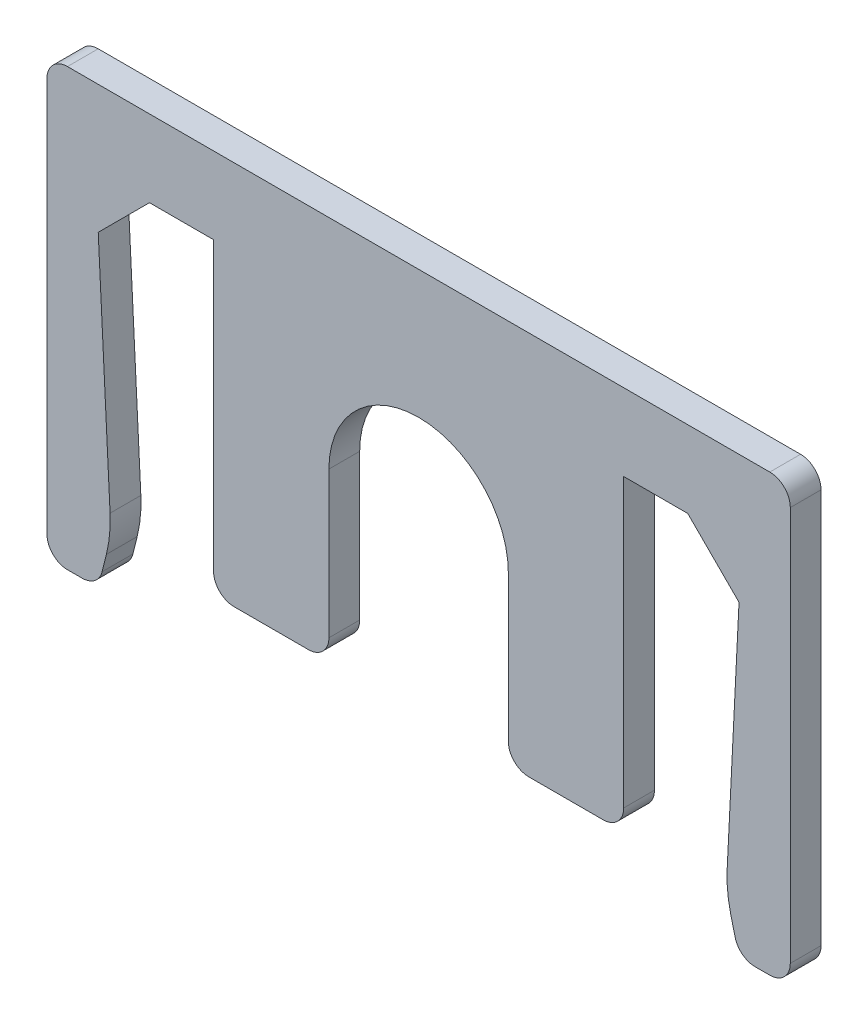
SolidWorks part; units mm, degrees
ref_plane "Front Plane" through (0, 0, 0) normal (0, 0, 1) x (1, 0, 0)
ref_plane "Top Plane" through (0, 0, 0) normal (0, 1, 0) x (1, 0, 0)
ref_plane "Right Plane" through (0, 0, 0) normal (1, 0, 0) x (0, 0, -1)
sketch "Sketch1" plane through (0, 0, 0) normal (0, 0, 1) x (1, 0, 0)
  line L0 (-12.5, 0) -> (-10.5, 0) construction
  line L1 (-10.5, 0) -> (-12.5, -2)
  line L2 (-12.5, -2) -> (-12.5, 0) construction
  line L3 (12.5, 0) -> (12.5, -2) construction
  line L4 (12.5, -2) -> (10.5, 0)
  line L5 (10.5, 0) -> (12.5, 0) construction
  line L6 (-12.5, -2) -> (-12, -12)
  line L7 (-12, -12) -> (-12.5, -14)
  line L8 (-12.5, -14) -> (-12.5, -2) construction
  line L9 (12.5, -2) -> (12.5, -14) construction
  line L10 (12.5, -14) -> (12, -12)
  line L11 (12, -12) -> (12.5, -2)
  line L12 (-10.5, 0) -> (-8, 0) construction
  line L13 (-3.5, -12) -> (3.5, -12) construction
  line L14 (-12.5, -14) -> (-14.5, -14)
  line L15 (-12.5, -14) -> (-12.5, -2) construction
  line L16 (-12.5, 3) -> (-14.5, 3)
  line L17 (-14.5, -14) -> (-14.5, 3)
  line L18 (12.5, -14) -> (14.5, -14)
  line L19 (12.5, -14) -> (12.5, -2) construction
  line L20 (12.5, 3) -> (14.5, 3)
  line L21 (14.5, -14) -> (14.5, 3)
  line L22 (-12.5, 3) -> (12.5, 3)
  line L23 (-12.5, 3) -> (-12.5, 0) construction
  line L24 (-10.5, 0) -> (-8, 0)
  line L25 (12.5, 3) -> (12.5, 0) construction
  line L26 (-3.5, -5.5) -> (3.5, -5.5) construction
  line L27 (-3.5, -5.5) -> (-3.5, -12)
  line L28 (-3.5, -12) -> (3.5, -12) construction
  line L29 (3.5, -5.5) -> (3.5, -12)
  line L30 (-8, -12) -> (-3.5, -12)
  line L31 (-8, -12) -> (-8, 0)
  line L32 (-8, 0) -> (8, 0) construction
  line L33 (8, -12) -> (8, 0)
  line L34 (-4.5, -3) -> (4.5, -3) construction
  line L35 (-4.5, -3) -> (-4.5, -12) construction
  line L36 (-4.5, -12) -> (-3.5, -12) construction
  line L37 (4.5, -3) -> (4.5, -12) construction
  line L38 (-4.5, -3) -> (4.5, -12) construction
  line L39 (-4.5, -12) -> (4.5, -3) construction
  line L40 (3.5, -12) -> (8, -12)
  line L41 (-3.5, -12) -> (3.5, -12) construction
  line L42 (3.5, -12) -> (4.5, -12) construction
  line L43 (-8, 0) -> (8, 0) construction
  line L44 (8, 0) -> (10.5, 0) construction
  line L45 (-8, 0) -> (8, 0) construction
  line L46 (8, 0) -> (10.5, 0)
  line L47 (-12.5, -2) -> (-12.5, 0) construction
  line L48 (-12.5, 0) -> (-12.5, 3) construction
  line L49 (-12.5, 0) -> (-10.5, 0) construction
  line L50 (12.5, 0) -> (12.5, 3) construction
  line L51 (10.5, 0) -> (12.5, 0) construction
  line L52 (12.5, -2) -> (12.5, 0) construction
  arc A0 (3.5, -5.5) -> (-3.5, -5.5) centre (0, -5.5) ccw
  arc A1 (-3.5, -5.5) -> (-1.2638, -8.7638) centre (0, -5.5) ccw construction
  arc A2 (-1.2638, -8.7638) -> (1.2638, -8.7638) centre (0, -5.5) ccw construction
  arc A3 (1.2638, -8.7638) -> (3.5, -5.5) centre (0, -5.5) ccw construction
  point P28 (0, 0)
  point P29 (0, -7.5)
  point P34 (5.8042, -3.4177)
  point P35 (-0.1925, -6.6497)
  point P37 (0, -6.898)
  point P38 (0, -7.5)
  point P39 (0, 0)
  point P40 (0, -7.5)
  point P41 (0, -5.5852)
  dimension "D12" = 7
  dimension "D1" = 2
  dimension "D2" = 2
  dimension "D3" = 2
  dimension "D4" = 0.5
  dimension "D5" = 2
  dimension "D6" = 10
  dimension "D7" = 0.5
  dimension "D8" = 21
  dimension "D9" = 2
  dimension "D10" = 2
  dimension "D11" = 3
  dimension "D13" = 16
  dimension "D14" = 9
  dimension "D15" = 9
  dimension "D16" = 10.5
  dimension "D17" = 2
extrude "Boss-Extrude1" add sketch "Sketch1" along normal blind 1.2
fillet "Fillet1" radius 5 2 edges at (-12, -12, 0.6) (12, -12, 0.6)
fillet "Fillet2" radius 0.8 10 edges at (14.5, 3, 0.6) (-14.5, 3, 0.6) (14.5, -14, 0.6) (-14.5, -14, 0.6) (12.5, -14, 0.6) (-12.5, -14, 0.6) (-8, -12, 0.6) (8, -12, 0.6) (3.5, -12, 0.6) (-3.5, -12, 0.6)
